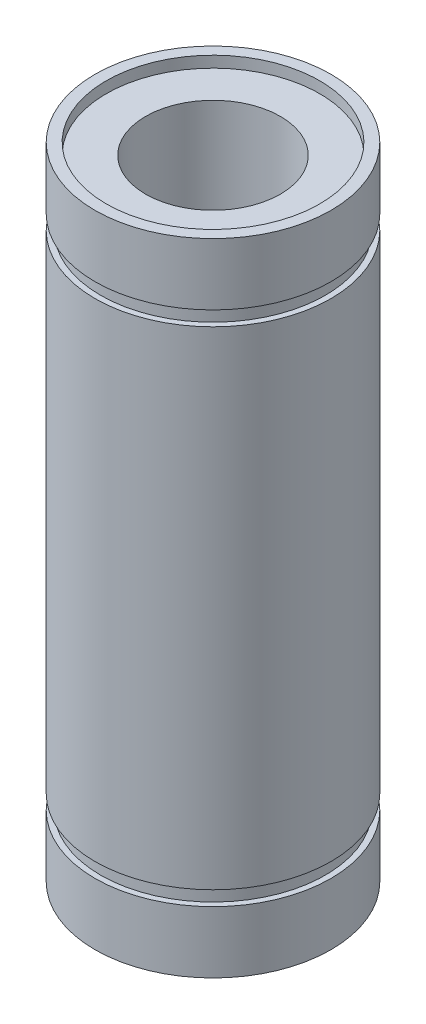
SolidWorks part; units mm, degrees
ref_plane "Front" through (0, 0, 0) normal (0, 0, 1) x (1, 0, 0)
ref_plane "Top" through (0, 0, 0) normal (0, 1, 0) x (1, 0, 0)
ref_plane "Right" through (0, 0, 0) normal (1, 0, 0) x (0, 0, -1)
sketch "Sketch1" plane through (0, 0, 0) normal (0, 1, 0) x (1, 0, 0)
  circle A0 centre (0, 0) radius 10.5
  circle A1 centre (0, 0) radius 6
  dimension "D1" = 12
  dimension "D2" = 21
extrude "Extrude1" add sketch "Sketch1" along normal blind 57
sketch "Sketch2" plane through (0, 57, 0) normal (0, 1, 0) x (1, 0, 0)
  circle A0 centre (0, 0) radius 9.5
  circle A1 centre (0, 0) radius 10.5 construction
  dimension "D1" = 1
extrude "Extrude2" cut sketch "Sketch2" against normal blind 1
sketch "Sketch3" plane through (0, 0, 0) normal (0, -1, 0) x (1, 0, 0)
  circle A0 centre (0, 0) radius 9.5
  circle A1 centre (0, 0) radius 10.5 construction
  dimension "D1" = 1
extrude "Extrude3" cut sketch "Sketch3" against normal blind 1
ref_plane "Plane1" through (0, 5.5, 0) normal (0, -1, 0) x (-1, 0, 0)
ref_plane "Plane2" through (0, 51.5, 0) normal (0, 1, 0) x (1, 0, 0)
sketch "Sketch4" plane through (0, 51.5, 0) normal (0, 1, 0) x (1, 0, 0)
  circle A0 centre (0, 0) radius 10
  dimension "D1" = 20
extrude "Extrude4" cut sketch "Sketch4" against normal blind 1.3 flip side to cut
sketch "Sketch5" plane through (0, 5.5, 0) normal (0, -1, 0) x (-1, 0, 0)
  circle A0 centre (0, 0) radius 10
  dimension "D1" = 20
extrude "Extrude5" cut sketch "Sketch5" against normal blind 1.3 flip side to cut
